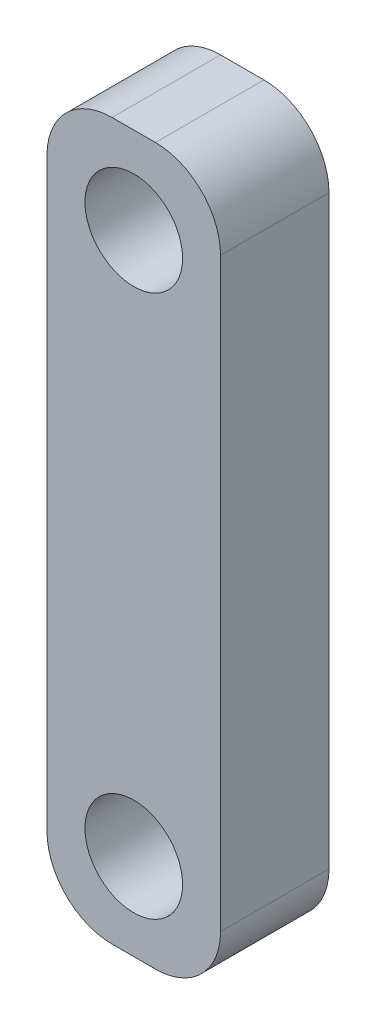
SolidWorks part; units mm, degrees
ref_plane "Front Plane" through (0, 0, 0) normal (0, 0, 1) x (1, 0, 0)
ref_plane "Top Plane" through (0, 0, 0) normal (0, 1, 0) x (1, 0, 0)
ref_plane "Right Plane" through (0, 0, 0) normal (1, 0, 0) x (0, 0, -1)
sketch "Sketch1" plane through (0, 0, 0) normal (0, 0, 1) x (1, 0, 0)
  line L1 (0, 0) -> (8, 0)
  line L2 (0, 0) -> (0, -33)
  line L3 (0, -33) -> (8, -33)
  line L4 (8, 0) -> (8, -33)
  circle A2 centre (4, -29) radius 2.25
  circle A3 centre (4, -4) radius 2.25
  dimension "D3" = 8
  dimension "D1" = 4.5
  dimension "D2" = 4
  dimension "D4" = 4
  dimension "D5" = 29
  dimension "D6" = 33
extrude "Boss-Extrude1" add sketch "Sketch1" along normal blind 5
fillet "Fillet1" radius 3 4 edges at (0, -33, 2.5) (8, -33, 2.5) (0, 0, 2.5) (8, 0, 2.5)
